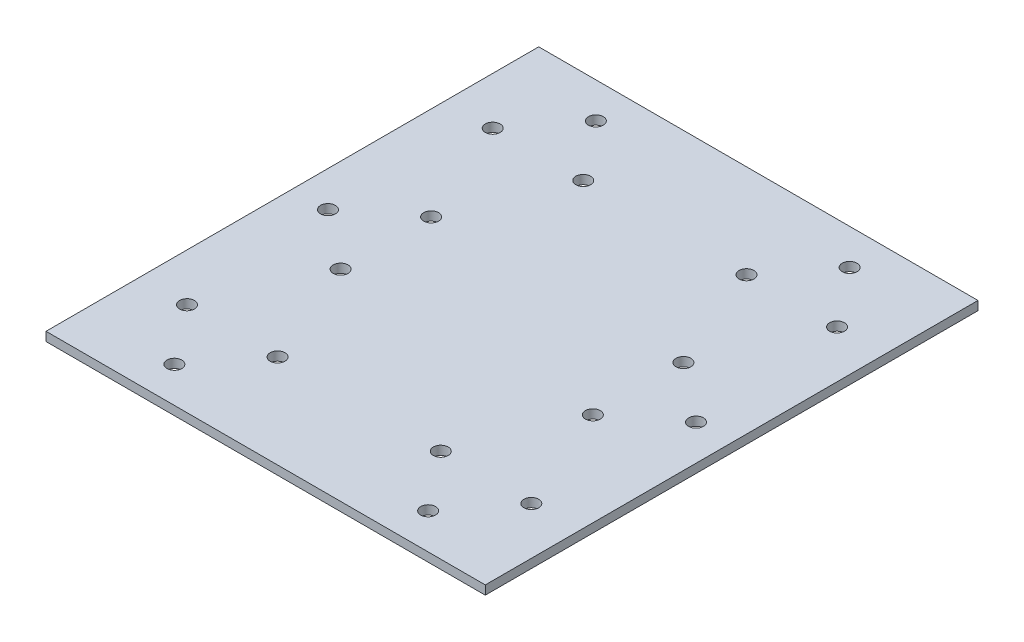
SolidWorks part; units mm, degrees
ref_plane "前视基准面" through (0, 0, 0) normal (0, 0, 1) x (1, 0, 0)
ref_plane "上视基准面" through (0, 0, 0) normal (0, 1, 0) x (1, 0, 0)
ref_plane "右视基准面" through (0, 0, 0) normal (1, 0, 0) x (0, 0, -1)
sketch "草图1" plane through (0, 0, 0) normal (0, 1, 0) x (1, 0, 0)
  line L5 (74, -83) -> (-74, -83)
  line L6 (74, -83) -> (74, 83)
  line L7 (74, 83) -> (-74, 83)
  line L8 (-74, -83) -> (-74, 83)
  line L9 (74, -83) -> (-74, 83) construction
  line L10 (74, 83) -> (-74, -83) construction
  point P0 (0, 0)
  dimension "D1" = 148
  dimension "D2" = 166
extrude "凸台-拉伸1" add sketch "草图1" along normal blind 3
sketch "草图2" plane through (0, 3, 0) normal (0, 1, 0) x (1, 0, 0)
  line L0 (-74, 83) -> (-74, -83) construction
  line L1 (74, 83) -> (-74, 83) construction
  line L2 (0, -80) -> (0, 83) construction
  line L4 (0, 83) -> (0, 0) construction
  line L6 (74, 80) -> (-74, 80) construction
  circle A0 centre (-58, 51.5) radius 2.5
  circle A1 centre (-27.5, 51.5) radius 2.5
  circle A2 centre (-27.5, -51.5) radius 2.5
  circle A3 centre (-58, -51.5) radius 2.5
  circle A4 centre (58, -51.5) radius 2.5
  circle A5 centre (27.5, -51.5) radius 2.5
  circle A6 centre (27.5, 51.5) radius 2.5
  circle A7 centre (58, 51.5) radius 2.5
  circle A16 centre (-42.75, 71) radius 2.5
  circle A17 centre (-42.75, -71) radius 2.5
  circle A18 centre (42.75, -71) radius 2.5
  circle A19 centre (42.75, 71) radius 2.5
  circle A22 centre (-62, 0) radius 2.5
  circle A23 centre (-42.5, -15.25) radius 2.5
  circle A24 centre (-42.5, 15.25) radius 2.5
  circle A25 centre (42.5, 15.25) radius 2.5
  circle A26 centre (42.5, -15.25) radius 2.5
  circle A27 centre (62, 0) radius 2.5
  point P15 (-74, 0)
  dimension "D1" = 5
  dimension "D2" = 5
  dimension "D3" = 30.5
  dimension "D4" = 16
  dimension "D5" = 31.5
  dimension "D6" = 5
  dimension "D7" = 5
  dimension "D8" = 12
  dimension "D9" = 5
  dimension "D10" = 5
  dimension "D11" = 15.25
  dimension "D12" = 15.25
  dimension "D13" = 30.5
  dimension "D14" = 12
  dimension "D15" = 15.25
  dimension "D16" = 31.5
  dimension "D17" = 31.5
  dimension "D18" = 80
extrude "切除-拉伸1" cut sketch "草图2" against normal through all
